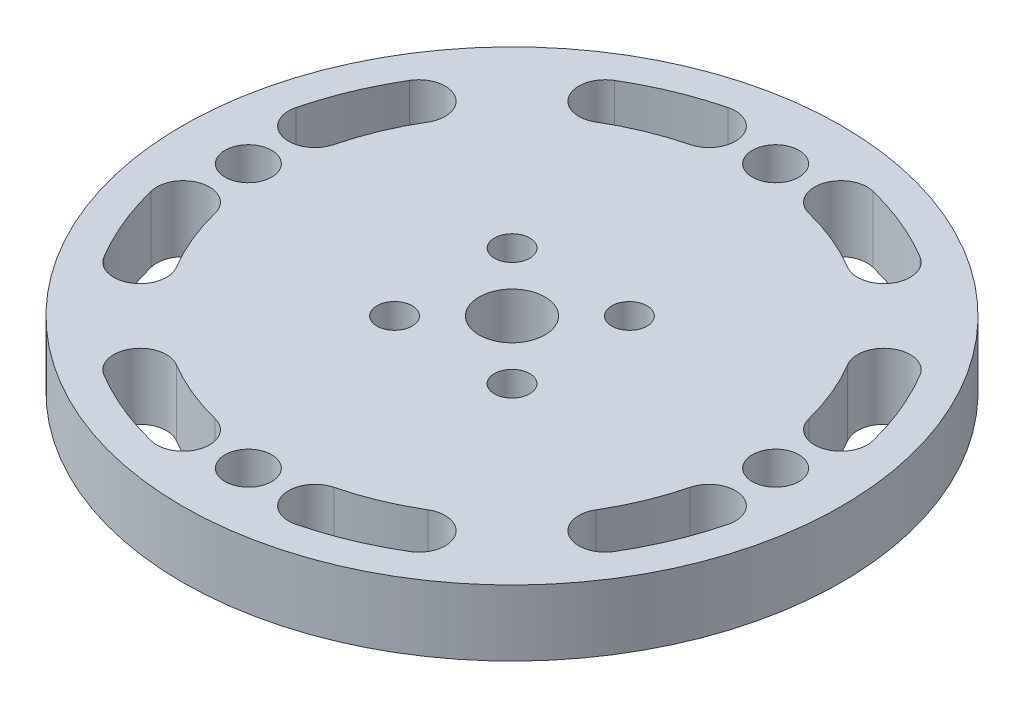
SolidWorks part; units mm, degrees
ref_plane "Front Plane" through (0, 0, 0) normal (0, 0, 1) x (1, 0, 0)
ref_plane "Top Plane" through (0, 0, 0) normal (0, 1, 0) x (1, 0, 0)
ref_plane "Right Plane" through (0, 0, 0) normal (1, 0, 0) x (0, 0, -1)
sketch "Sketch1" plane through (0, 0, 0) normal (0, 1, 0) x (1, 0, 0)
  line L4 (44.7892, 14.5529) -> (0, 47.0942) construction
  line L5 (0, 47.0942) -> (-44.7892, 14.5529) construction
  line L9 (-44.7892, 14.5529) -> (-27.6813, -38.1) [skipped]
  line L10 (-27.6813, -38.1) -> (27.6813, -38.1) [skipped]
  line L11 (27.6813, -38.1) -> (44.7892, 14.5529) [skipped]
  line L14 (-31.5904, -3.1799) -> (-27.8167, -15.3066) construction
  circle A0 centre (0, 0) radius 31.75
  dimension "D1" = 63.5
extrude "Boss-Extrude1" add sketch "Sketch1" along normal blind 6.35
sketch "Sketch2" plane through (0, 6.35, 0) normal (0, 1, 0) x (1, 0, 0)
  circle A0 centre (0, 0) radius 3.175
  circle A1 centre (-5.655, 5.6624) radius 1.7
  circle A2 centre (5.655, 5.655) radius 1.7
  circle A3 centre (5.655, -5.655) radius 1.7
  circle A4 centre (-5.6624, -5.655) radius 1.7
  point P11 (0, 0)
  point P13 (2.2684, 5.3762)
  point P14 (5.3763, -4.1069)
  dimension "D1" = 6.35
  dimension "D2" = 3.4
  dimension "D3" = 3.4
  dimension "D4" = 3.4
  dimension "D5" = 3.4
  dimension "D6" = 16
  dimension "D7" = 16
  dimension "D8" = 5.655
  dimension "D9" = 5.655
  dimension "D10" = 5.655
  dimension "D11" = 5.655
  dimension "D12" = 5.655
  dimension "D13" = 5.655
extrude "Cut-Extrude1" cut sketch "Sketch2" against normal through all
sketch "Sketch3" plane through (0, 6.35, 0) normal (0, 1, 0) x (1, 0, 0)
  line L0 (0, 0) -> (0, -31.75) construction
  line L1 (0, -31.75) -> (0, 31.75) construction
  line L2 (0, 31.75) -> (0, 0) construction
  line L3 (0, 0) -> (31.75, 0) construction
  line L4 (31.75, 0) -> (-31.75, 0) construction
  line L5 (-31.75, 0) -> (0, 0) construction
  line L6 (0, 0) -> (22.4506, -22.4506) construction
  line L7 (0, 0) -> (-22.4506, 22.4506) construction
  line L8 (-22.4506, 22.4506) -> (0, 0) construction
  line L9 (0, 0) -> (22.4506, 22.4506) construction
  line L10 (22.4506, 22.4506) -> (-22.4506, -22.4506) construction
  arc A0 (-13.424, 22.4043) -> (-6.35, 25.3344) centre (0, 0) cw construction
  arc A1 (-6.9675, 27.7982) -> (-14.7295, 24.5831) centre (0, 0) ccw
  arc A2 (-5.7325, 22.8707) -> (-12.1185, 20.2255) centre (0, 0) ccw
  arc A3 (-5.7325, 22.8707) -> (-6.9675, 27.7982) centre (-6.35, 25.3344) ccw
  arc A4 (-14.7295, 24.5831) -> (-12.1185, 20.2255) centre (-13.424, 22.4043) ccw
  circle A5 centre (0, 0) radius 31.75 construction
  arc A6 (-22.4043, 13.424) -> (-25.3344, 6.35) centre (0, 0) ccw construction
  arc A7 (-27.7982, 6.9675) -> (-24.5831, 14.7295) centre (0, 0) cw
  arc A8 (-22.8707, 5.7325) -> (-20.2255, 12.1185) centre (0, 0) cw
  arc A9 (-22.8707, 5.7325) -> (-27.7982, 6.9675) centre (-25.3344, 6.35) cw
  arc A10 (-24.5831, 14.7295) -> (-20.2255, 12.1185) centre (-22.4043, 13.424) cw
  arc A11 (-22.4043, -13.424) -> (-25.3344, -6.35) centre (0, 0) cw construction
  arc A12 (-27.7982, -6.9675) -> (-24.5831, -14.7295) centre (0, 0) ccw
  arc A13 (-22.8707, -5.7325) -> (-20.2255, -12.1185) centre (0, 0) ccw
  arc A14 (-22.8707, -5.7325) -> (-27.7982, -6.9675) centre (-25.3344, -6.35) ccw
  arc A15 (-24.5831, -14.7295) -> (-20.2255, -12.1185) centre (-22.4043, -13.424) ccw
  arc A16 (-13.424, -22.4043) -> (-6.35, -25.3344) centre (0, 0) ccw construction
  arc A17 (-6.9675, -27.7982) -> (-14.7295, -24.5831) centre (0, 0) cw
  arc A18 (-5.7325, -22.8707) -> (-12.1185, -20.2255) centre (0, 0) cw
  arc A19 (-5.7325, -22.8707) -> (-6.9675, -27.7982) centre (-6.35, -25.3344) cw
  arc A20 (-14.7295, -24.5831) -> (-12.1185, -20.2255) centre (-13.424, -22.4043) cw
  arc A21 (13.424, -22.4043) -> (6.35, -25.3344) centre (0, 0) cw construction
  arc A22 (6.9675, -27.7982) -> (14.7295, -24.5831) centre (0, 0) ccw
  arc A23 (5.7325, -22.8707) -> (12.1185, -20.2255) centre (0, 0) ccw
  arc A24 (5.7325, -22.8707) -> (6.9675, -27.7982) centre (6.35, -25.3344) ccw
  arc A25 (14.7295, -24.5831) -> (12.1185, -20.2255) centre (13.424, -22.4043) ccw
  arc A26 (22.4043, -13.424) -> (25.3344, -6.35) centre (0, 0) ccw construction
  arc A27 (27.7982, -6.9675) -> (24.5831, -14.7295) centre (0, 0) cw
  arc A28 (22.8707, -5.7325) -> (20.2255, -12.1185) centre (0, 0) cw
  arc A29 (22.8707, -5.7325) -> (27.7982, -6.9675) centre (25.3344, -6.35) cw
  arc A30 (24.5831, -14.7295) -> (20.2255, -12.1185) centre (22.4043, -13.424) cw
  arc A31 (22.4043, 13.424) -> (25.3344, 6.35) centre (0, 0) cw construction
  arc A32 (27.7982, 6.9675) -> (24.5831, 14.7295) centre (0, 0) ccw
  arc A33 (22.8707, 5.7325) -> (20.2255, 12.1185) centre (0, 0) ccw
  arc A34 (22.8707, 5.7325) -> (27.7982, 6.9675) centre (25.3344, 6.35) ccw
  arc A35 (24.5831, 14.7295) -> (20.2255, 12.1185) centre (22.4043, 13.424) ccw
  arc A36 (13.424, 22.4043) -> (6.35, 25.3344) centre (0, 0) ccw construction
  arc A37 (6.9675, 27.7982) -> (14.7295, 24.5831) centre (0, 0) cw
  arc A38 (5.7325, 22.8707) -> (12.1185, 20.2255) centre (0, 0) cw
  arc A39 (5.7325, 22.8707) -> (6.9675, 27.7982) centre (6.35, 25.3344) cw
  arc A40 (14.7295, 24.5831) -> (12.1185, 20.2255) centre (13.424, 22.4043) cw
  point P4 (-9.995, 24.13)
  point P24 (-24.13, 9.995)
  point P31 (-24.13, -9.995)
  point P38 (-9.995, -24.13)
  point P45 (9.995, -24.13)
  point P52 (24.13, -9.995)
  point P59 (24.13, 9.995)
  point P66 (9.995, 24.13)
  dimension "D2" = 5.08
  dimension "D1" = 24.13
  dimension "D3" = 6.35
  dimension "D4" = 6.35
  dimension "D5" = 45
extrude "Cut-Extrude2" cut sketch "Sketch3" against normal through all
sketch "Sketch4" plane through (0, 6.35, 0) normal (0, 1, 0) x (1, 0, 0)
  circle A0 centre (0, -25.4) radius 2.2479
  circle A1 centre (25.4, 0) radius 2.2479
  circle A2 centre (-25.4, 0) radius 2.2479
  circle A3 centre (0, 25.4) radius 2.2479
  point P8 (0, 0)
  point P12 (-26.0275, 0.3904)
  dimension "D1" = 4.4958
  dimension "D2" = 4.4958
  dimension "D3" = 4.4958
  dimension "D4" = 4.4958
  dimension "D5" = 25.4
  dimension "D6" = 25.4
  dimension "D9" = 50.8
  dimension "D7" = 50.8
  dimension "D8" = 25.4
extrude "Cut-Extrude3" cut sketch "Sketch4" against normal through all
